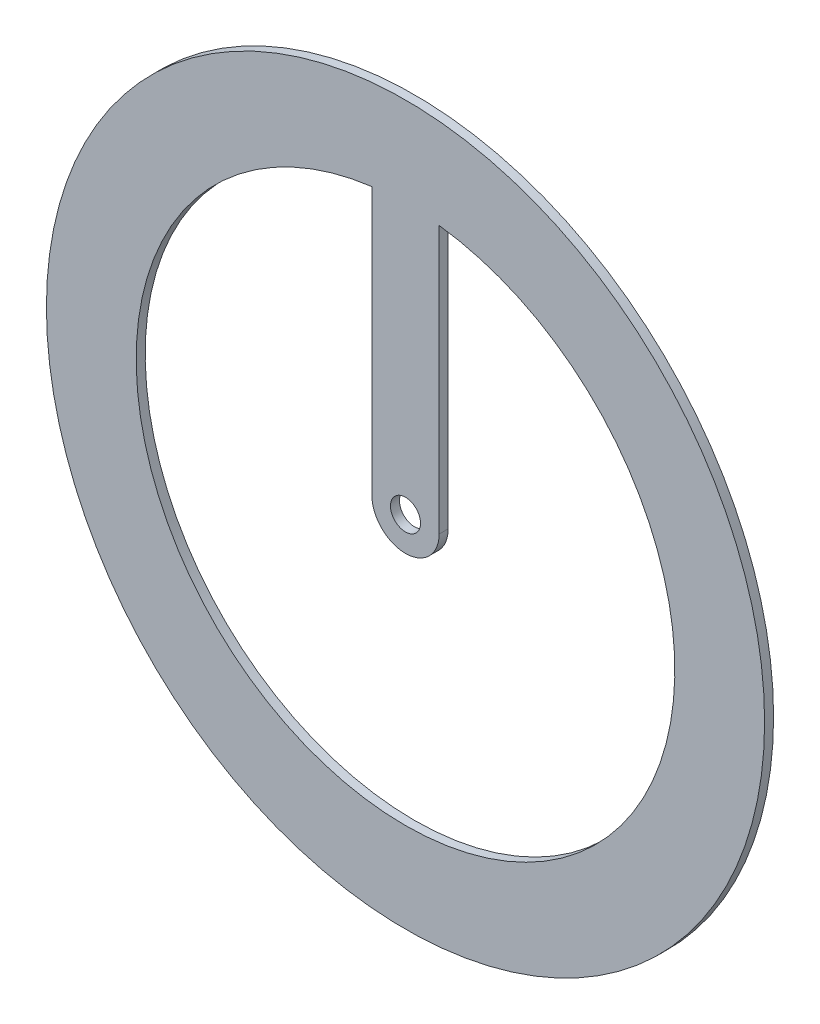
SolidWorks part; units mm, degrees
ref_plane "Front Plane" through (0, 0, 0) normal (0, 0, 1) x (1, 0, 0)
ref_plane "Top Plane" through (0, 0, 0) normal (0, 1, 0) x (1, 0, 0)
ref_plane "Right Plane" through (0, 0, 0) normal (1, 0, 0) x (0, 0, -1)
sketch "Sketch1" plane through (0, 0, 0) normal (0, 0, 1) x (1, 0, 0)
  line L0 (-9.525, 0) -> (-9.525, 75.6023)
  line L1 (9.525, 0) -> (9.525, 75.6023)
  circle A0 centre (0, 0) radius 101.6
  arc A1 (-9.525, 75.6023) -> (9.525, 75.6023) centre (0, 0) ccw
  arc A2 (-9.525, 0) -> (9.525, 0) centre (0, 0) ccw
  circle A3 centre (0, 0) radius 76.2 construction
  circle A4 centre (0, 0) radius 4.2496
  dimension "D1" = 203.2
  dimension "D3" = 19.05
  dimension "D2" = 25.4
extrude "Boss-Extrude1" add sketch "Sketch1" along normal blind 2.54
